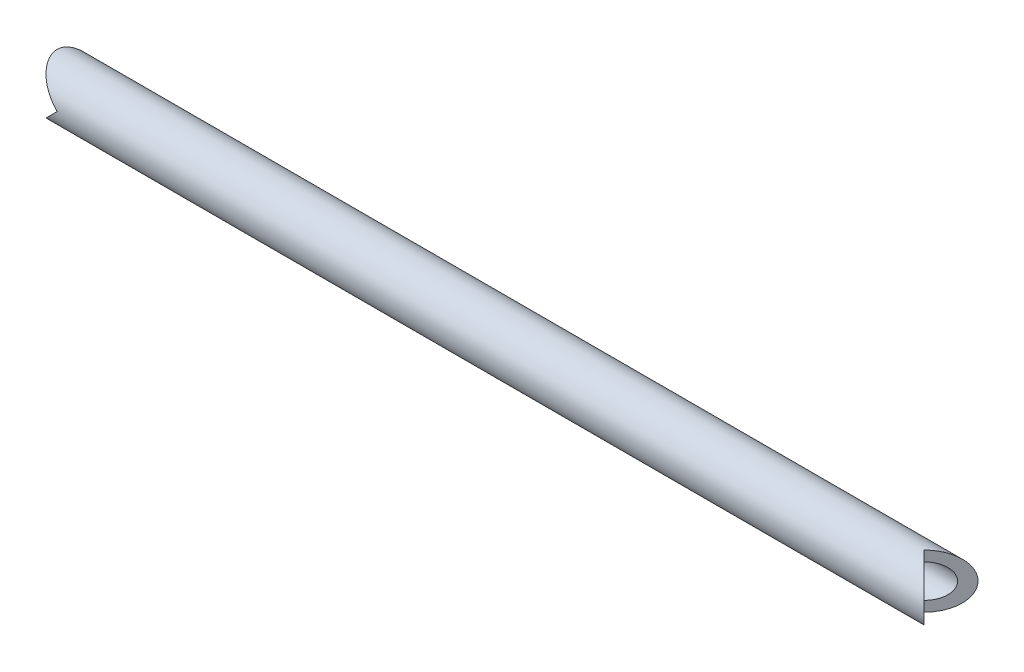
SolidWorks part; units mm, degrees
material "PE Low/Medium Density"
ref_plane "Front Plane" through (0, 0, 0) normal (0, 0, 1) x (1, 0, 0)
ref_plane "Top Plane" through (0, 0, 0) normal (0, 1, 0) x (1, 0, 0)
ref_plane "Right Plane" through (0, 0, 0) normal (1, 0, 0) x (0, 0, -1)
sketch "Sketch1" plane through (0, 0, 0) normal (1, 0, 0) x (0, 0, -1)
  circle A0 centre (0, 0) radius 2.0066
  circle A1 centre (0, 0) radius 1.2446
  dimension "D1" = 4.0132
  dimension "D2" = 0.762
extrude "Boss-Extrude1" add sketch "Sketch1" along normal blind 66.675
sketch "Sketch3" plane through (0, 0, 0) normal (0, 0, 1) x (1, 0, 0)
  line L0 (0, 2.0066) -> (2.0066, 0)
  line L1 (2.0066, 0) -> (0, -2.0066)
  line L2 (0, -2.0066) -> (0, 2.0066)
  line L3 (33.3375, 2.0066) -> (33.3375, 10.949) construction
  line L4 (66.675, 2.0066) -> (0, 2.0066) construction
  dimension "D1" = 90
extrude "Cut-Extrude2" cut sketch "Sketch3" against normal through all both and the other way through all
sketch "Sketch4" plane through (0, 0, 0) normal (0, 1, 0) x (1, 0, 0)
  line L0 (66.675, 2.0066) -> (64.6684, 0)
  line L1 (64.6684, 0) -> (66.675, -2.0066)
  line L2 (66.675, -2.0066) -> (66.675, 2.0066)
  point P6 (66.675, 0)
  dimension "D1" = 90
extrude "Cut-Extrude3" cut sketch "Sketch4" along normal through all both and the other way through all
